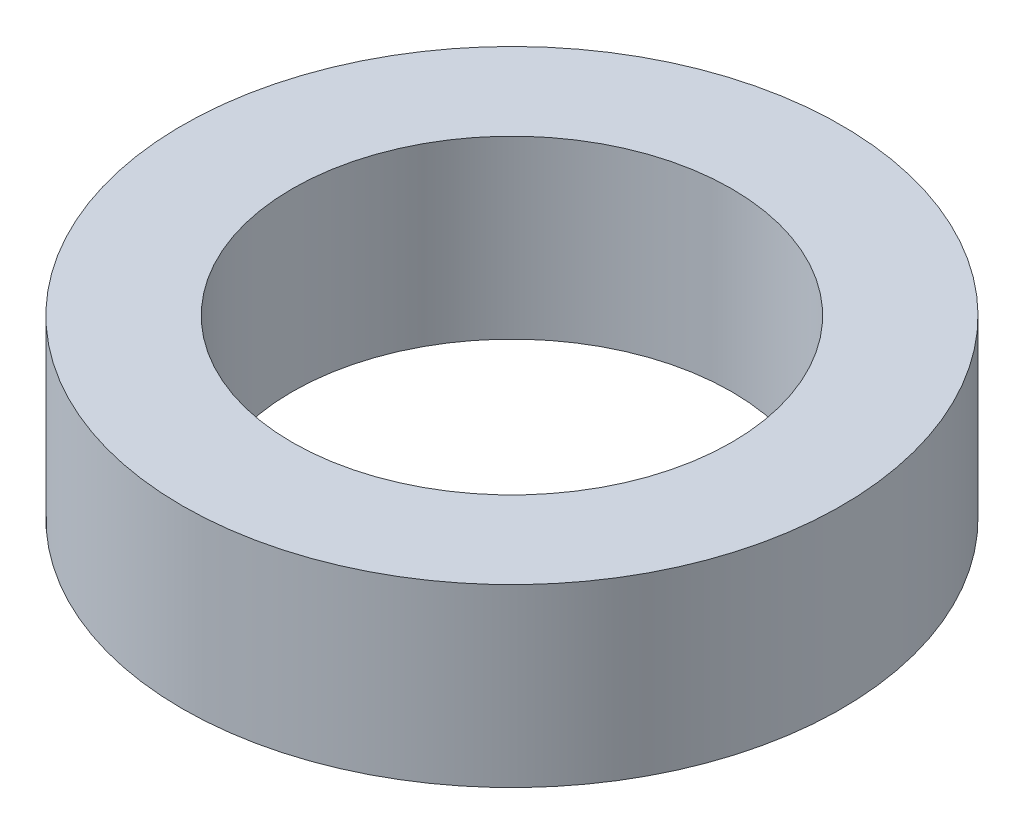
SolidWorks part; units mm, degrees
material "1023 Carbon Steel Sheet (SS)"
ref_plane "Front Plane" through (0, 0, 0) normal (0, 0, 1) x (1, 0, 0)
ref_plane "Top Plane" through (0, 0, 0) normal (0, 1, 0) x (1, 0, 0)
ref_plane "Right Plane" through (0, 0, 0) normal (1, 0, 0) x (0, 0, -1)
sketch "Sketch1" plane through (0, 0, 0) normal (0, 1, 0) x (1, 0, 0)
  circle A0 centre (0, 0) radius 7.5
  circle A1 centre (0, 0) radius 5
  dimension "D1" = 15
  dimension "D2" = 10
extrude "Boss-Extrude1" add sketch "Sketch1" along normal mid plane 4
